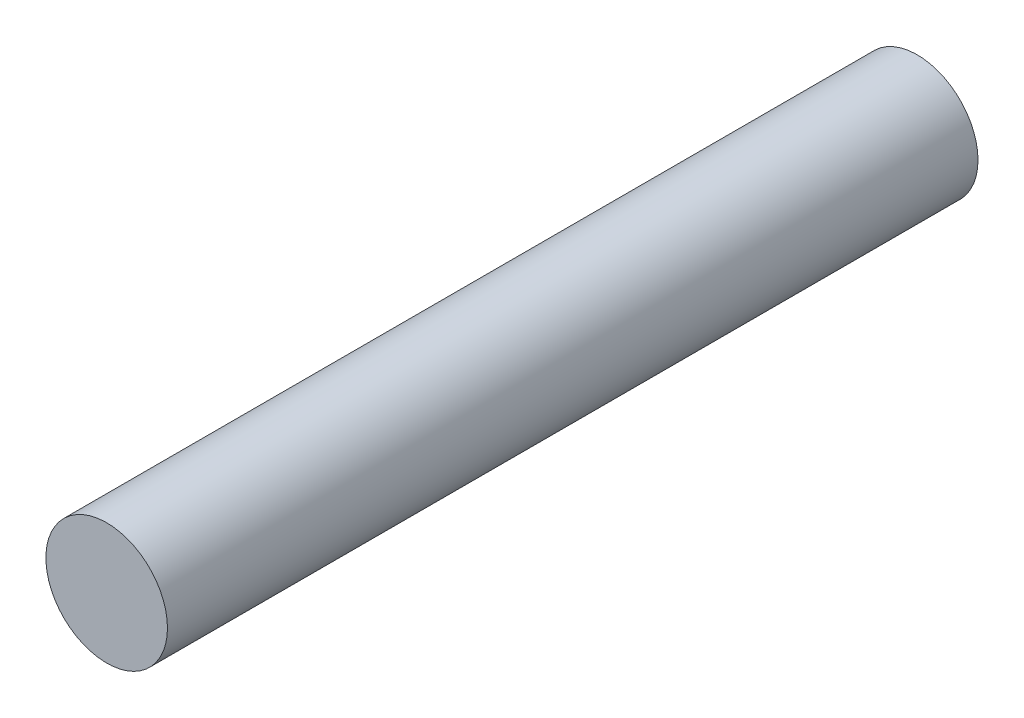
SolidWorks part; units mm, degrees
ref_plane "Front Plane" through (0, 0, 0) normal (0, 0, 1) x (1, 0, 0)
ref_plane "Top Plane" through (0, 0, 0) normal (0, 1, 0) x (1, 0, 0)
ref_plane "Right Plane" through (0, 0, 0) normal (1, 0, 0) x (0, 0, -1)
sketch "Sketch1" plane through (0, 0, 0) normal (0, 0, 1) x (1, 0, 0)
  circle A0 centre (0, 0) radius 1.5
  dimension "D1" = 3
extrude "Boss-Extrude1" add sketch "Sketch1" along normal blind 20
